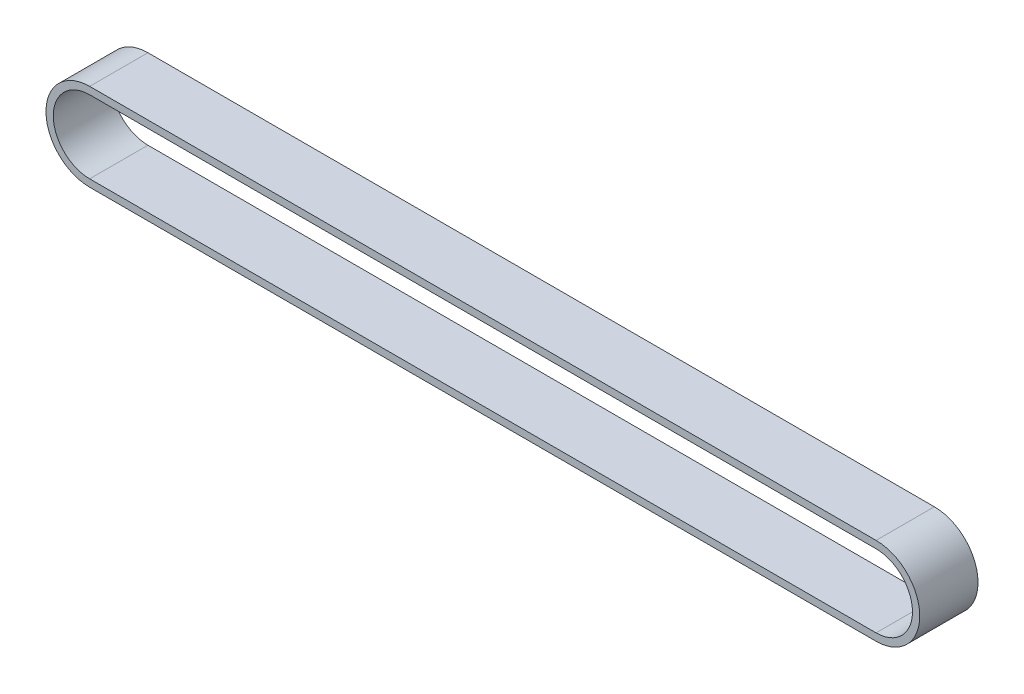
SolidWorks part; units mm, degrees
material "Borracha de silicone"
ref_plane "Plano frontal" through (0, 0, 0) normal (0, 0, 1) x (1, 0, 0)
ref_plane "Plano superior" through (0, 0, 0) normal (0, 1, 0) x (1, 0, 0)
ref_plane "Plano direito" through (0, 0, 0) normal (1, 0, 0) x (0, 0, -1)
sketch "Esboço1" plane through (0, 0, 0) normal (0, 0, 1) x (1, 0, 0)
  line L0 (-18.8263, 0) -> (89.1737, 0) construction
  line L1 (-18.8263, 0) -> (89.1737, 0) construction
  line L2 (-18.8263, 5) -> (89.1737, 5)
  line L3 (-18.8263, -5) -> (89.1737, -5)
  line L4 (-18.8263, 6) -> (89.1737, 6)
  line L5 (-18.8263, -6) -> (89.1737, -6)
  arc A0 (-18.8263, 5) -> (-18.8263, -5) centre (-18.8263, 0) ccw
  arc A1 (89.1737, -5) -> (89.1737, 5) centre (89.1737, 0) ccw
  arc A2 (89.1737, -6) -> (89.1737, 6) centre (89.1737, 0) ccw
  arc A3 (-18.8263, 6) -> (-18.8263, -6) centre (-18.8263, 0) ccw
  point P3 (35.1737, 0)
  dimension "D1" = 5
  dimension "D2" = 108
  dimension "D3" = 1
extrude "Ressalto-extrusão1" add sketch "Esboço1" along normal blind 8
